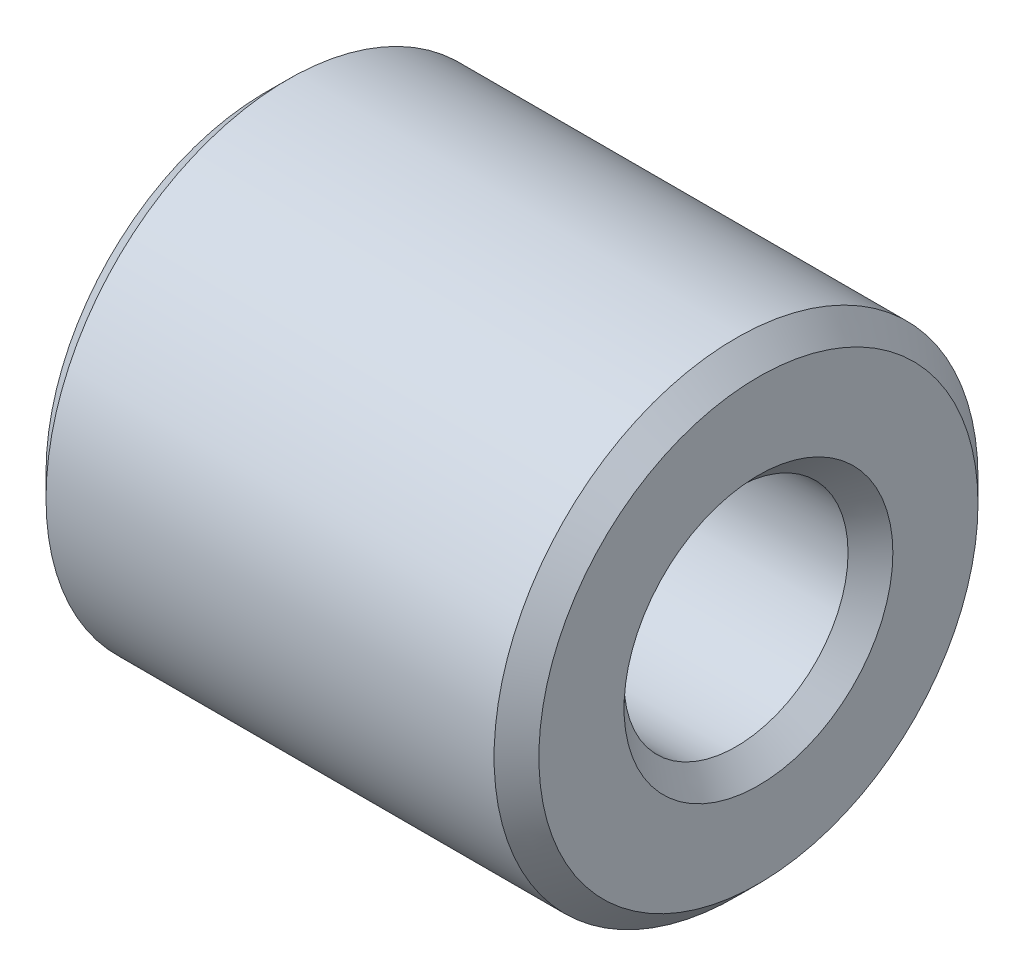
SolidWorks part; units mm, degrees
ref_plane "Front Plane" through (0, 0, 0) normal (0, 0, 1) x (1, 0, 0)
ref_plane "Top Plane" through (0, 0, 0) normal (0, 1, 0) x (1, 0, 0)
ref_plane "Right Plane" through (0, 0, 0) normal (1, 0, 0) x (0, 0, -1)
sketch "Sketch1" plane through (0, 0, 0) normal (0, 0, 1) x (1, 0, 0)
  line L1 (5.5, 2.5) -> (5.5, 5.4)
  line L2 (0, 0) -> (-50000, 0) construction
  line L3 (0, 0) -> (0, 50000) construction
  line L5 (-5.5, 5.4) -> (5.5, 5.4)
  line L6 (-5.5, 5.4) -> (-5.5, 2.5)
  line L18 (-5.5, 2.5) -> (5.5, 2.5)
  circle A2 centre (2.15, 6.289) radius 0.889 construction
  dimension "D1" = 11
  dimension "D4" = 2.5
  dimension "D2" = 5.5
  dimension "D3" = 5.4
revolve "Revolve1" add sketch "Sketch1" angle 360 about L2
sketch "Sketch2" plane through (0, 0, 0) normal (0, 1, 0) x (1, 0, 0)
  line L2 (-5.5, 5.4) -> (-5.5, -5.4) construction
  circle A0 centre (-2.75, 0) radius 1.5
  dimension "D1" = 3
  dimension "D2" = 2.75
extrude "Cut-Extrude1" cut sketch "Sketch2" against normal blind 10
chamfer "Chamfer1" distance 0.5 angle 45 4 edges at (-5.5, 0, -2.5) (5.5, 0, -2.5) (-5.5, 0, -5.4) (5.5, 0, -5.4)
